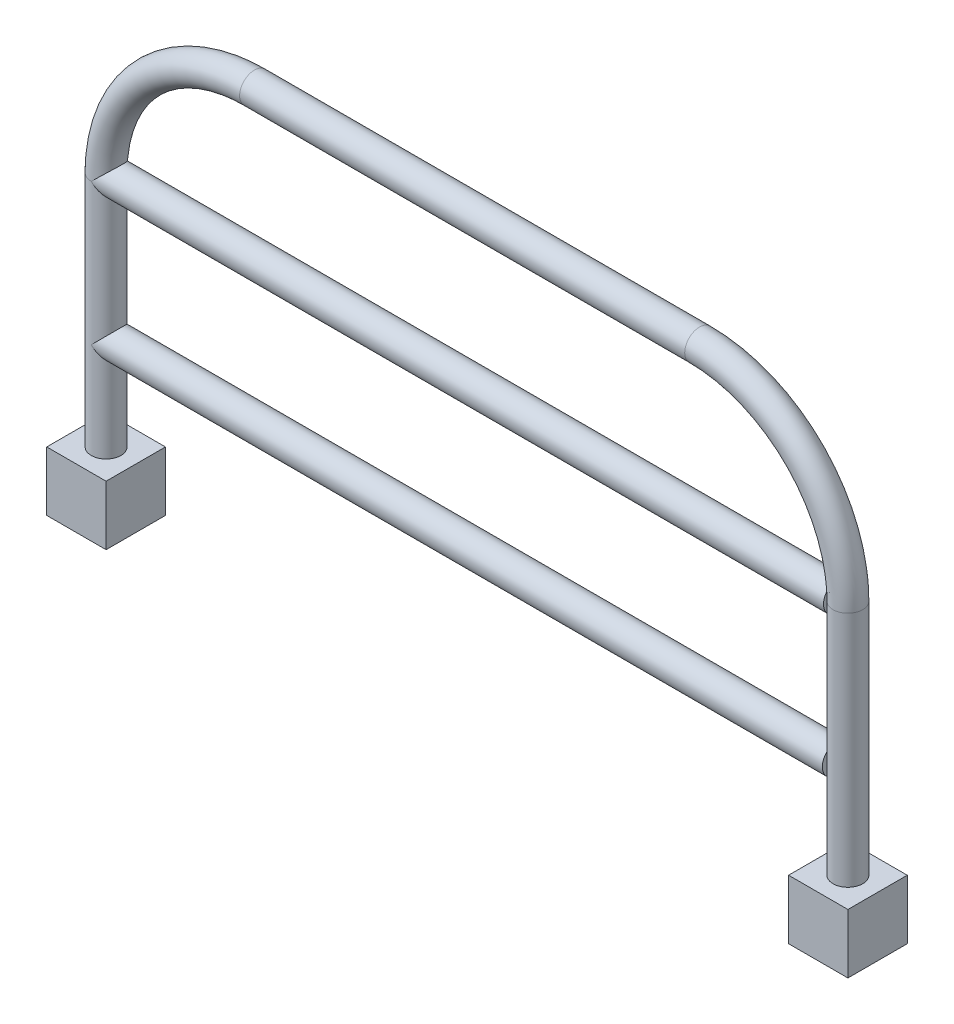
SolidWorks part; units mm, degrees
ref_plane "Front Plane" through (0, 0, 0) normal (0, 0, 1) x (1, 0, 0)
ref_plane "Top Plane" through (0, 0, 0) normal (0, 1, 0) x (1, 0, 0)
ref_plane "Right Plane" through (0, 0, 0) normal (1, 0, 0) x (0, 0, -1)
sketch "Sketch1" plane through (0, 0, 0) normal (0, 0, 1) x (1, 0, 0)
  line L0 (0, 0) -> (0, 203.2)
  line L1 (635, 203.2) -> (635, 0)
  line L3 (127, 330.2) -> (508, 330.2)
  arc A0 (508, 330.2) -> (635, 203.2) centre (508, 203.2) cw
  arc A1 (0, 203.2) -> (127, 330.2) centre (127, 203.2) cw
  dimension "D1" = 127
  dimension "D2" = 635
  dimension "D3" = 203.2
sketch "Sketch2" plane through (0, 0, 0) normal (0, 1, 0) x (1, 0, 0)
  circle A0 centre (0, 0) radius 12.7
  dimension "D1" = 25.4
sweep "Sweep1" add profiles "Sketch2" path "Sketch1"
sketch "Sketch3" plane through (0, 0, 0) normal (0, -1, 0) x (1, 0, 0)
  line L1 (25.4, 25.4) -> (-25.4, 25.4)
  line L2 (25.4, 25.4) -> (25.4, -25.4)
  line L3 (25.4, -25.4) -> (-25.4, -25.4)
  line L4 (-25.4, 25.4) -> (-25.4, -25.4)
  line L5 (25.4, 25.4) -> (-25.4, -25.4) construction
  line L6 (25.4, -25.4) -> (-25.4, 25.4) construction
  line L7 (660.4, 25.4) -> (609.6, 25.4)
  line L8 (660.4, 25.4) -> (660.4, -25.4)
  line L9 (660.4, -25.4) -> (609.6, -25.4)
  line L10 (609.6, 25.4) -> (609.6, -25.4)
  line L11 (660.4, 25.4) -> (609.6, -25.4) construction
  line L12 (660.4, -25.4) -> (609.6, 25.4) construction
  point P0 (0, 0)
  point P6 (635, 0)
  dimension "D1" = 50.8
  dimension "D2" = 50.8
  dimension "D3" = 50.8
  dimension "D4" = 50.8
extrude "Boss-Extrude1" add sketch "Sketch3" along normal blind 50.8
sketch "Sketch4" plane through (0, 0, 0) normal (1, 0, 0) x (0, 0, -1)
  line L0 (-12.7, 203.2) -> (12.7, 203.2) construction
  circle A0 centre (0, 203.2) radius 12.7
  dimension "D1" = 25.4
extrude "Boss-Extrude2" add sketch "Sketch4" along normal blind 626.8
sketch "Sketch5" plane through (0, 0, 0) normal (1, 0, 0) x (0, 0, -1)
  circle A0 centre (0, 82.0991) radius 12.7
  dimension "D1" = 25.4
extrude "Boss-Extrude3" add sketch "Sketch5" along normal blind 625.8
